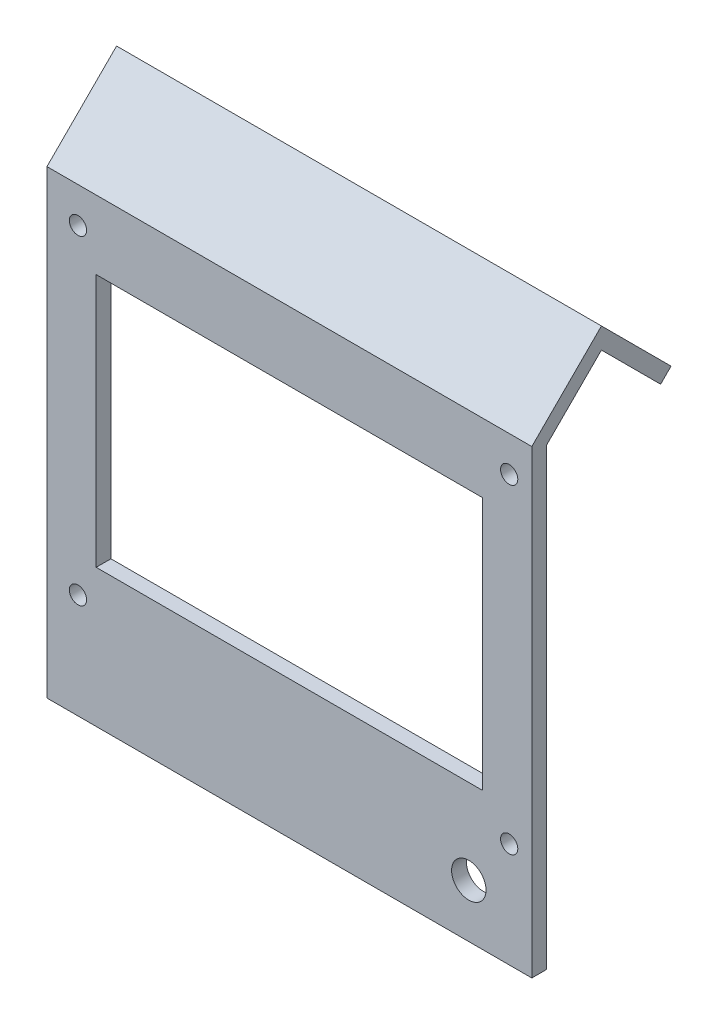
SolidWorks part; units mm, degrees
ref_plane "Front Plane" through (0, 0, 0) normal (0, 0, 1) x (1, 0, 0)
ref_plane "Top Plane" through (0, 0, 0) normal (0, 1, 0) x (1, 0, 0)
ref_plane "Right Plane" through (0, 0, 0) normal (1, 0, 0) x (0, 0, -1)
sketch "Sketch1" plane through (0, 0, 0) normal (0, 0, 1) x (1, 0, 0)
  line L1 (0, 0) -> (98.5, 0)
  line L2 (0, 0) -> (0, 93.5)
  line L3 (0, 93.5) -> (98.5, 93.5)
  line L4 (98.5, 0) -> (98.5, 93.5)
  line L5 (10, 79.5) -> (88.5, 79.5)
  line L6 (10, 79.5) -> (10, 28)
  line L7 (10, 28) -> (88.5, 28)
  line L8 (88.5, 79.5) -> (88.5, 28)
  dimension "D1" = 10
  dimension "D2" = 14
  dimension "D3" = 51.5
  dimension "D4" = 78.5
  dimension "D5" = 10
  dimension "D6" = 28
extrude "Boss-Extrude1" add sketch "Sketch1" along normal blind 3
sketch "Sketch2" plane through (0, 0, 3) normal (0, 0, 1) x (1, 0, 0)
  line L0 (93.9, 93.5) -> (93.9, 0) construction
  line L1 (98.5, 93.5) -> (0, 93.5) construction
  line L2 (0, 0) -> (98.5, 0) construction
  line L3 (88.5, 28) -> (88.5, 79.5) construction
  line L4 (98.5, 86.3) -> (0, 86.3) construction
  line L5 (98.5, 0) -> (98.5, 93.5) construction
  line L6 (0, 93.5) -> (0, 0) construction
  line L7 (98.5, 21.3) -> (0, 21.3) construction
  line L8 (6.3, 21.3) -> (6.3, 86.3) construction
  line L9 (88.5, 79.5) -> (10, 79.5) construction
  line L10 (10, 79.5) -> (10, 28) construction
  circle A0 centre (85.7, 10.8) radius 3.5
  circle A1 centre (93.9, 86.3) radius 1.75
  circle A2 centre (93.9, 21.3) radius 1.75
  circle A3 centre (6.3, 21.3) radius 1.75
  circle A4 centre (6.3, 86.3) radius 1.75
  point P24 (0, 0)
  point P26 (6.1677, 84.2627)
  point P27 (5.0931, 84.2435)
  dimension "D1" = 7
  dimension "D3" = 3.5
  dimension "D2" = 5.4
  dimension "D4" = 87.6
  dimension "D5" = 65
  dimension "D6" = 6.8
  dimension "D7" = 72.2
  dimension "D8" = 79.2
extrude "Cut-Extrude1" cut sketch "Sketch2" against normal up to next
sketch "Sketch5" plane through (0, 0, 0) normal (-1, 0, 0) x (0, 0, 1)
  line L0 (3, 93.5) -> (-11.1421, 107.6421)
  line L2 (0.8787, 91.3787) -> (-13.2635, 105.5208)
  line L4 (3, 93.5) -> (3, 0) construction
  line L5 (-13.2635, 105.5208) -> (-11.1421, 107.6421)
  line L7 (3, 93.5) -> (0.8787, 91.3787)
  point P7 (0.9542, 91.5525)
  dimension "D1" = 225
  dimension "D2" = 90
  dimension "D3" = 20
  dimension "D4" = 90
  dimension "D5" = 3
extrude "Boss-Extrude4" add sketch "Sketch5" against normal blind 98.5
sketch "Sketch6" plane through (0, 0, 0) normal (-1, 0, 0) x (0, 0, 1)
  line L0 (-11.1421, 107.6421) -> (-25.2843, 93.5)
  line L1 (-25.2843, 93.5) -> (-23.163, 91.3787)
  line L2 (-23.163, 91.3787) -> (-9.0208, 105.5208)
  line L3 (3, 93.5) -> (-11.1421, 107.6421) construction
  line L4 (-9.0208, 105.5208) -> (-11.1421, 107.6421)
  dimension "D1" = 3
  dimension "D2" = 20
extrude "Boss-Extrude5" add sketch "Sketch6" against normal blind 98.5
